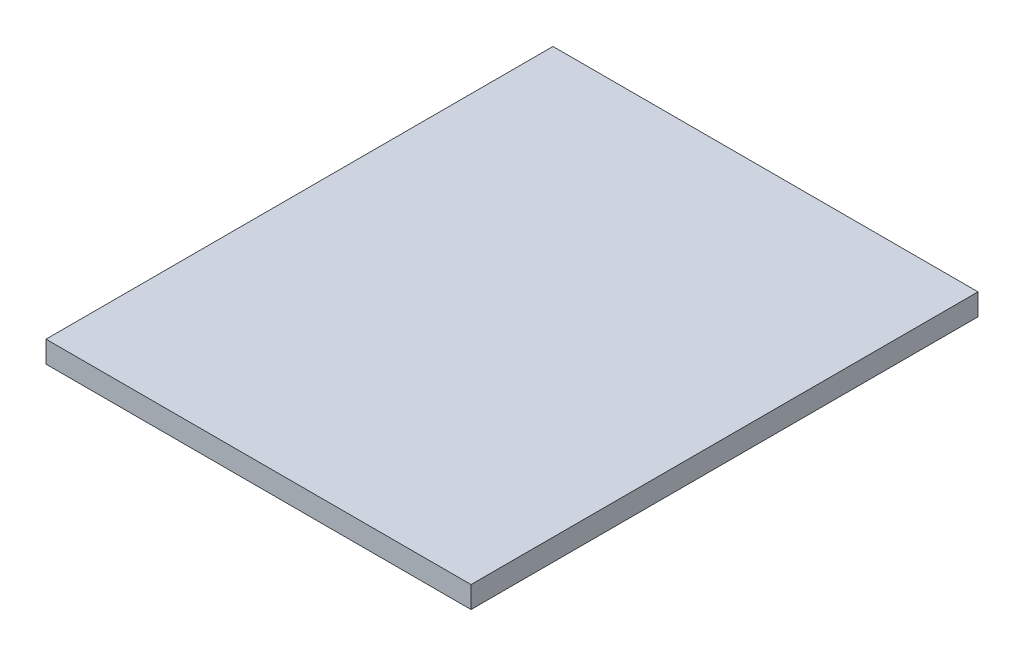
SolidWorks part; units mm, degrees
ref_plane "Front Plane" through (0, 0, 0) normal (0, 0, 1) x (1, 0, 0)
ref_plane "Top Plane" through (0, 0, 0) normal (0, 1, 0) x (1, 0, 0)
ref_plane "Right Plane" through (0, 0, 0) normal (1, 0, 0) x (0, 0, -1)
sketch "Sketch1" plane through (0, 0, 0) normal (0, 1, 0) x (1, 0, 0)
  line L1 (0, 0) -> (30.6, 0)
  line L2 (0, 0) -> (0, 36.5)
  line L3 (0, 36.5) -> (30.6, 36.5)
  line L4 (30.6, 0) -> (30.6, 36.5)
  dimension "D1" = 30.6
  dimension "D2" = 36.5
extrude "Boss-Extrude1" add sketch "Sketch1" along normal blind 1.56 contours L2 L3 L4 L1
